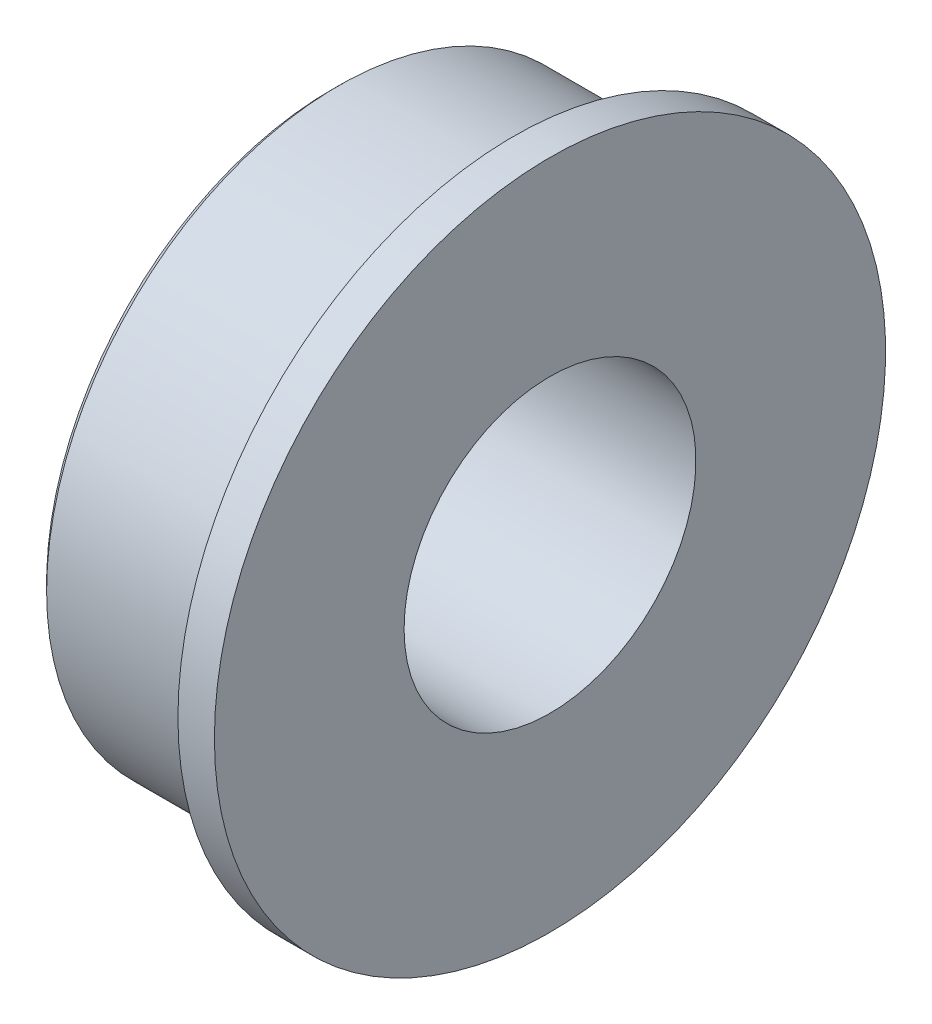
SolidWorks part; units mm, degrees
material "1060 合金"
ref_plane "前视基准面" through (0, 0, 0) normal (0, 0, 1) x (1, 0, 0)
ref_plane "上视基准面" through (0, 0, 0) normal (0, 1, 0) x (1, 0, 0)
ref_plane "右视基准面" through (0, 0, 0) normal (1, 0, 0) x (0, 0, -1)
other "Configuration Table"
sketch "草图1" plane through (0, 0, 0) normal (0, 0, 1) x (1, 0, 0)
  line L0 (0, 0) -> (9560.7378, 0) construction
  line L1 (0, 0) -> (0, 2) construction
  line L2 (0, 2) -> (0, 4)
  line L3 (0, 4) -> (2.5, 4)
  line L4 (2.5, 4) -> (2.5, 4.6)
  line L5 (2.5, 4.6) -> (3, 4.6)
  line L6 (3, 4.6) -> (3, 2)
  line L7 (3, 2) -> (0, 2)
  dimension "D1" = 2
  dimension "D2" = 4
  dimension "D3" = 4.6
  dimension "D4" = 3
  dimension "D5" = 0.5
revolve "旋转1" add sketch "草图1" angle 360 about L0
chamfer "倒角1" distance 0.1 angle 45 1 edges at (0, 0, 4)
